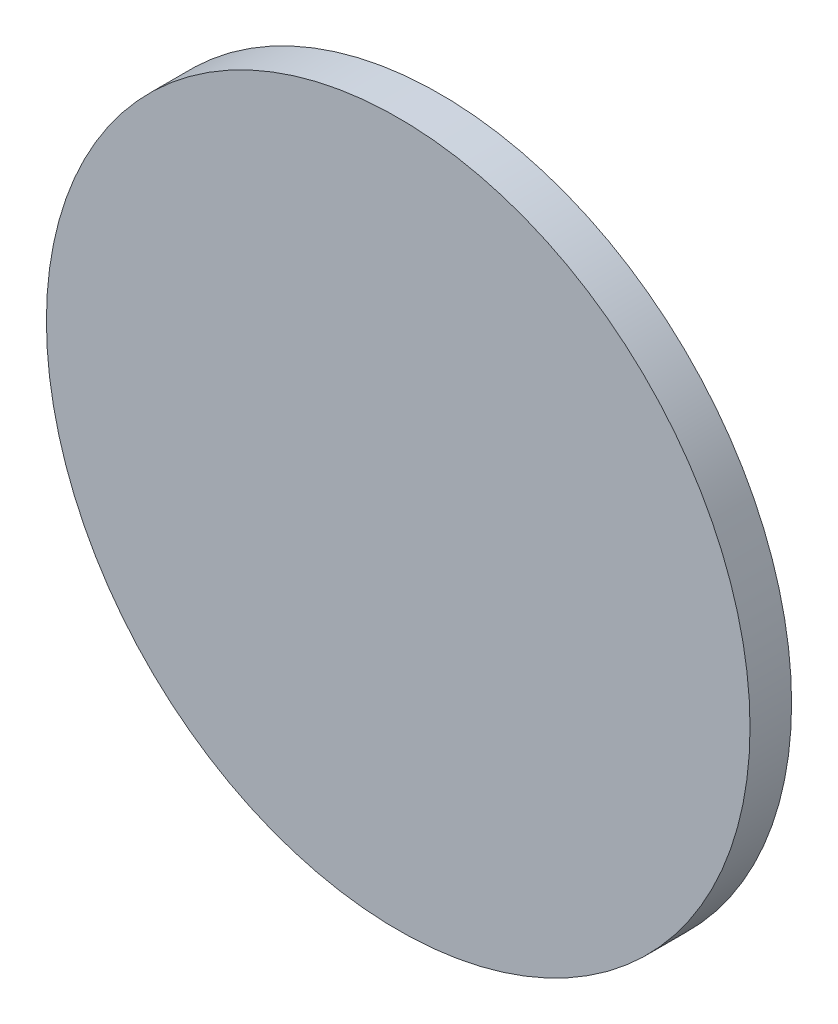
SolidWorks part; units mm, degrees
ref_plane "Front" through (0, 0, 0) normal (0, 0, 1) x (1, 0, 0)
ref_plane "Top" through (0, 0, 0) normal (0, 1, 0) x (1, 0, 0)
ref_plane "Right" through (0, 0, 0) normal (1, 0, 0) x (0, 0, -1)
sketch "Sketch1" plane through (0, 0, 0) normal (0, 0, 1) x (1, 0, 0)
  circle A0 centre (0, 0) radius 25.4
  dimension "D1" = 50.8
extrude "Boss-Extrude1" add sketch "Sketch1" along normal blind 3
